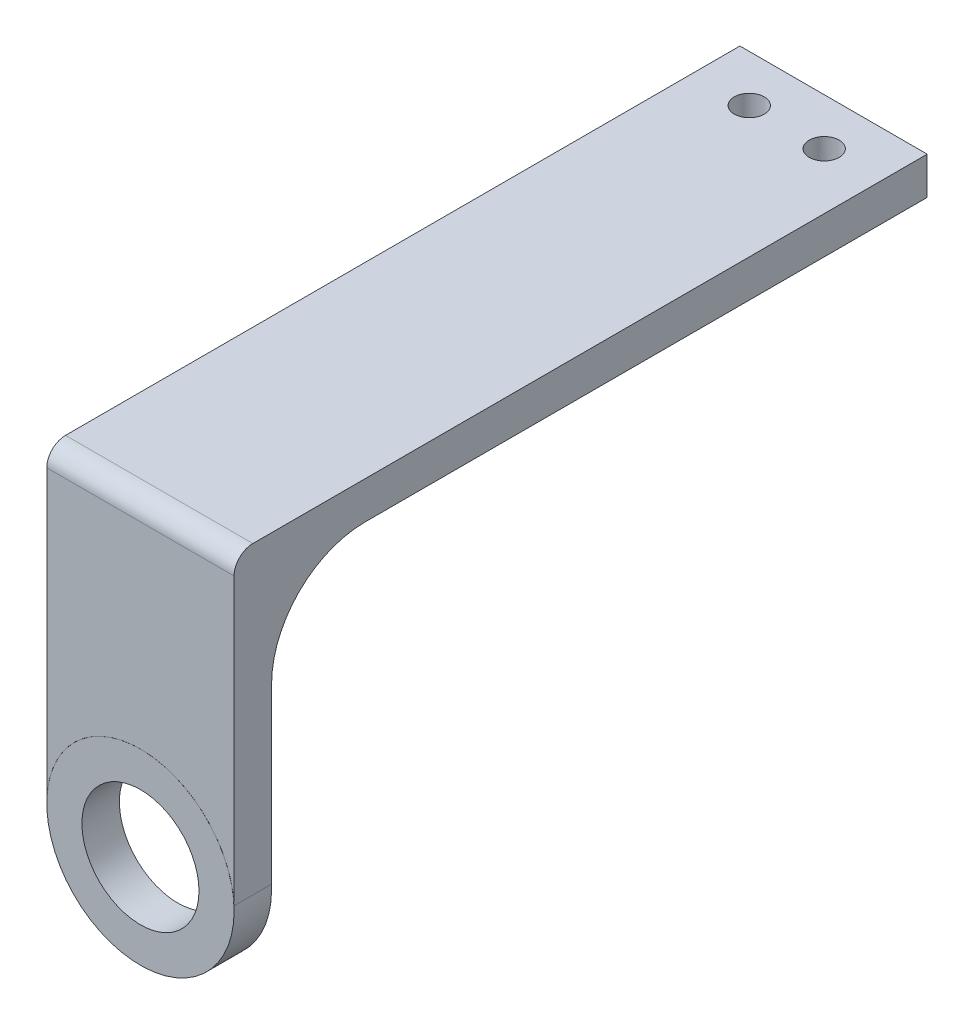
SolidWorks part; units mm, degrees
ref_plane "Alzado" through (0, 0, 0) normal (0, 0, 1) x (1, 0, 0)
ref_plane "Planta" through (0, 0, 0) normal (0, 1, 0) x (1, 0, 0)
ref_plane "Vista lateral" through (0, 0, 0) normal (1, 0, 0) x (0, 0, -1)
sketch "Croquis1" plane through (0, 0, 0) normal (0, 0, 1) x (1, 0, 0)
  line L0 (-10, 0) -> (-10, 33)
  line L1 (-10, 33) -> (10, 33)
  line L2 (10, 33) -> (10, 0.503)
  circle A0 centre (0, 0) radius 6.25
  circle A1 centre (0, 0) radius 10
  arc A2 (-10, 0) -> (10, 0.503) centre (0.0063, 0) cw
  dimension "D1" = 3.75
  dimension "D2" = 12.5
  dimension "D3" = 33
  dimension "D4" = 20
extrude "Saliente-Extruir1" add sketch "Croquis1" along normal blind 4 contours L0 A2 L2 L1 | A1 A0
sketch "Croquis2" plane through (0, 0, 0) normal (0, 0, -1) x (-1, 0, 0)
  line L0 (-10, 33) -> (-10, 29)
  line L1 (-10, 33) -> (-10, 0.503) construction
  line L2 (-10, 29) -> (10, 29)
  line L3 (10, 0) -> (10, 33) construction
  line L4 (10, 29) -> (10, 33)
  line L5 (10, 33) -> (-10, 33)
  line L6 (10, 33) -> (-10, 33) construction
  line L10 (10, 0) -> (10, 33)
  line L11 (10, 33) -> (-10, 33)
  line L12 (-10, 33) -> (-10, 0.503)
  line L13 (10, 0) -> (10, 33)
  line L14 (10, 33) -> (-10, 33)
  line L15 (-10, 33) -> (-10, 0.503)
  arc A1 (10, 0) -> (-10, 0.503) centre (-0.0063, 0) ccw
  arc A2 (10, 0) -> (-10, 0.503) centre (-0.0063, 0) ccw
  line M6 (10, 0) -> (10, 33)
  line M7 (10, 33) -> (-10, 33)
  line M8 (-10, 33) -> (-10, 0.503)
  dimension "D1" = 4
  dimension "D2" = 0
  dimension "D3" = 20
extrude "Saliente-Extruir2" add sketch "Croquis2" along normal blind 70 contours L2 M8 M6 M7
sketch "Croquis3" plane through (0, 33, 0) normal (0, 1, 0) x (1, 0, 0)
  line L0 (0, 70) -> (0, 65) construction
  line L1 (-10, 70) -> (10, 70) construction
  line L2 (-4, 65) -> (4, 65)
  circle A0 centre (-4, 65) radius 1.6
  circle A1 centre (4, 65) radius 1.6
  point P8 (0, 65)
  dimension "D2" = 3.2
  dimension "D3" = 3.2
  dimension "D1" = 5
  dimension "D4" = 8
extrude "Cortar-Extruir1" cut sketch "Croquis3" against normal blind 10
fillet "Redondeo1" radius 10 1 edges at (0, 29, 0)
fillet "Redondeo2" radius 2 1 edges at (0, 33, 4)
